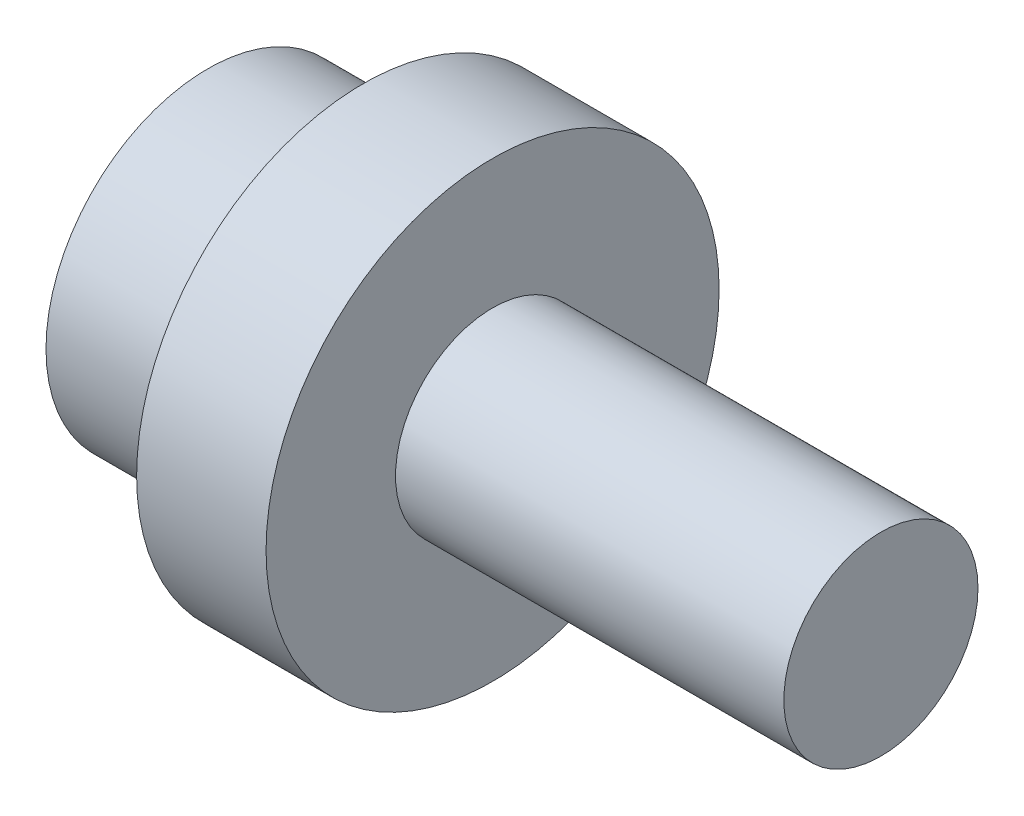
SolidWorks part; units mm, degrees
material "11 500"
ref_plane "Přední rovina" through (0, 0, 0) normal (0, 0, 1) x (1, 0, 0)
ref_plane "Vrchní rovina" through (0, 0, 0) normal (0, 1, 0) x (1, 0, 0)
ref_plane "Pravá rovina" through (0, 0, 0) normal (1, 0, 0) x (0, 0, -1)
sketch "Skica1" plane through (0, 0, 0) normal (0, 0, 1) x (1, 0, 0)
  line L0 (0, 0) -> (0, 12.5)
  line L1 (0, 12.5) -> (12, 12.5)
  line L2 (12, 12.5) -> (12, 17.5)
  line L3 (12, 17.5) -> (22, 17.5)
  line L4 (22, 17.5) -> (22, 7.5)
  line L5 (22, 7.5) -> (52, 7.5)
  line L6 (52, 7.5) -> (52, 0)
  line L7 (52, 0) -> (0, 0)
  line L8 (0, 0) -> (-16150.7148, 0) construction
  dimension "D1" = 25
  dimension "D2" = 35
  dimension "D3" = 15
  dimension "D4" = 30
  dimension "D5" = 10
  dimension "D6" = 12
revolve "Rotovat1" add sketch "Skica1" angle 360 about L8
